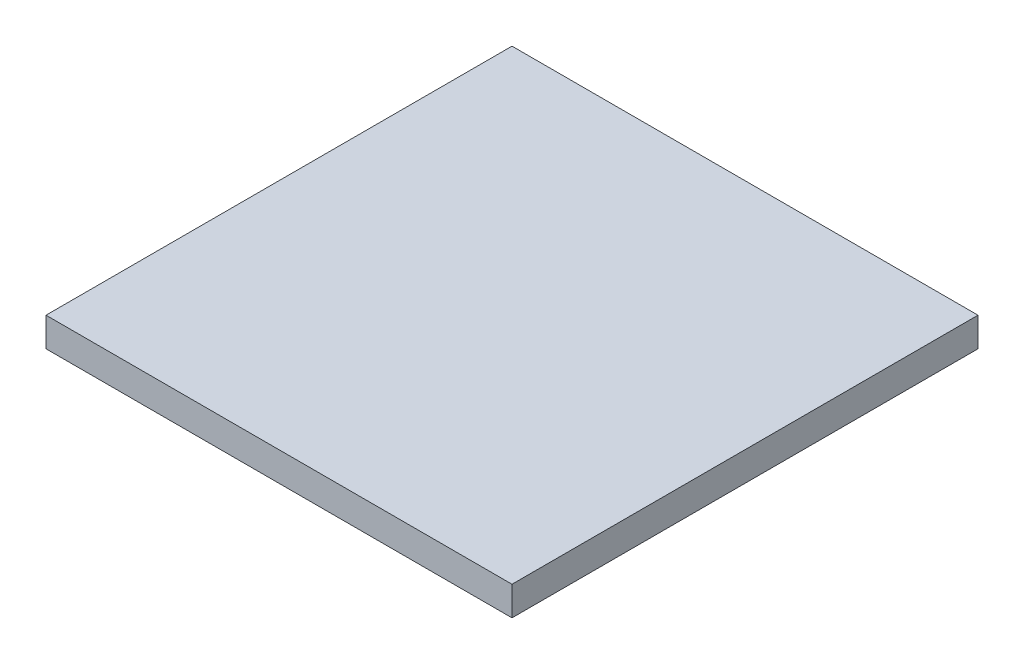
SolidWorks part; units mm, degrees
material "Nylon 101"
ref_plane "Front Plane" through (0, 0, 0) normal (0, 0, 1) x (1, 0, 0)
ref_plane "Top Plane" through (0, 0, 0) normal (0, 1, 0) x (1, 0, 0)
ref_plane "Right Plane" through (0, 0, 0) normal (1, 0, 0) x (0, 0, -1)
sketch "Sketch1" plane through (0, 0, 0) normal (0, 1, 0) x (1, 0, 0)
  line L1 (0, 0) -> (25.4, 0)
  line L2 (0, 0) -> (0, 25.4)
  line L3 (0, 25.4) -> (25.4, 25.4)
  line L4 (25.4, 0) -> (25.4, 25.4)
  dimension "D1" = 25.4
  dimension "D2" = 25.4
extrude "Boss-Extrude1" add sketch "Sketch1" along normal blind 1.5875
